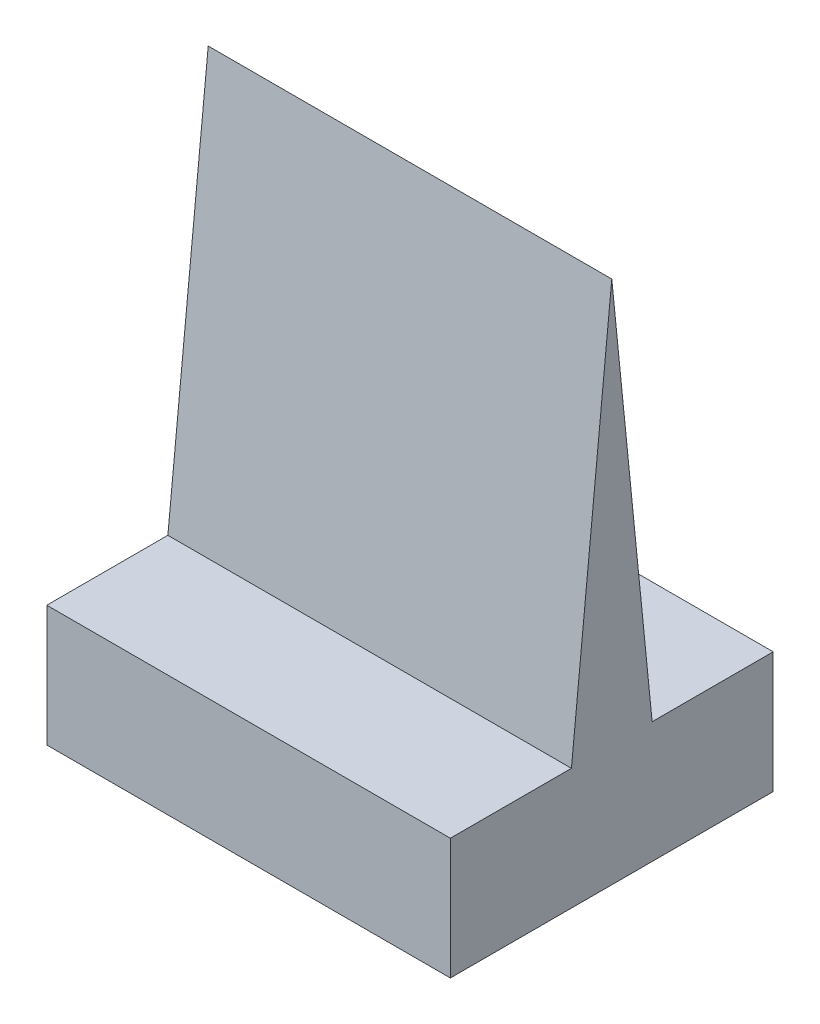
SolidWorks part; units mm, degrees
material "6061 Alloy"
ref_plane "Front Plane" through (0, 0, 0) normal (0, 0, 1) x (1, 0, 0)
ref_plane "Top Plane" through (0, 0, 0) normal (0, 1, 0) x (1, 0, 0)
ref_plane "Right Plane" through (0, 0, 0) normal (1, 0, 0) x (0, 0, -1)
sketch "Sketch1" plane through (0, 0, 0) normal (1, 0, 0) x (0, 0, -1)
  line L0 (1.27, 3.81) -> (0, 16.51)
  line L1 (0, 16.51) -> (-1.27, 3.81)
  line L2 (1.27, 3.81) -> (5.08, 3.81)
  line L3 (5.08, 3.81) -> (5.08, 0)
  line L4 (5.08, 0) -> (-5.08, 0)
  line L5 (0, -3.2801) -> (0, 12.0766) construction
  line L6 (-5.08, 3.81) -> (-5.08, 0)
  line L7 (-1.27, 3.81) -> (-5.08, 3.81)
  point P10 (0, 0)
  dimension "D1" = 2.54
  dimension "D2" = 12.7
  dimension "D3" = 3.81
  dimension "D4" = 5.08
extrude "Boss-Extrude1" add sketch "Sketch1" along normal blind 12.7
sketch "Sketch2" plane through (0, 0, 0) normal (0, -1, 0) x (1, 0, 0)
  line L0 (12.7, 5.08) -> (0, 5.08) construction
  circle A0 centre (6.35, 0) radius 2.54
  point P5 (6.35, 5.08)
  dimension "D1" = 5.08
extrude "Cut-Extrude1" cut sketch "Sketch2" against normal blind 3.175
